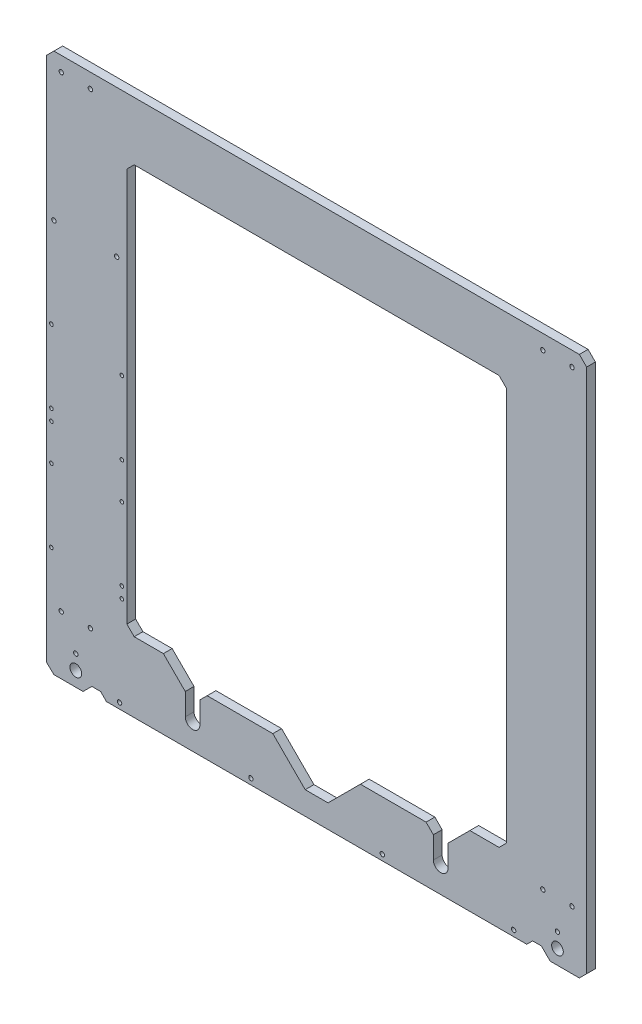
SolidWorks part; units mm, degrees
material "Lega 1060"
ref_plane "Piano frontale" through (0, 0, 0) normal (0, 0, 1) x (1, 0, 0)
ref_plane "Piano superiore" through (0, 0, 0) normal (0, 1, 0) x (1, 0, 0)
ref_plane "Piano destro" through (0, 0, 0) normal (1, 0, 0) x (0, 0, -1)
sketch "FRAME" plane through (0, 0, 0) normal (0, 0, 1) x (1, 0, 0)
  line L0 (0, 4.8083) -> (0, 365)
  line L1 (5, 370) -> (365, 370)
  line L2 (370, 365) -> (370, 5)
  line L3 (365, 0) -> (345, 0)
  line L4 (5, 0) -> (0, 4.8083)
  line L5 (0, 4.8083) -> (0, 365)
  line L6 (0, 365) -> (5, 370)
  line L7 (5, 370) -> (365, 370)
  line L8 (365, 370) -> (370, 365)
  line L9 (370, 365) -> (370, 5)
  line L10 (370, 5) -> (365, 0)
  line L11 (365, 0) -> (345, 0)
  line L12 (345, 0) -> (343, 2)
  line L13 (329, 2) -> (41, 2)
  line L14 (27, 2) -> (25, 0)
  line L15 (25, 0) -> (5, 0)
  line L16 (95, 20) -> (95, 35)
  line L17 (95, 35) -> (80, 50)
  line L18 (80, 50) -> (60, 50)
  line L19 (60, 50) -> (55, 55)
  line L20 (55, 55) -> (55, 325)
  line L21 (55, 325) -> (60, 330)
  line L22 (60, 330) -> (310, 330)
  line L23 (310, 330) -> (315, 325)
  line L24 (315, 325) -> (315, 55)
  line L25 (315, 55) -> (310, 50)
  line L26 (105, 20) -> (105, 35)
  line L27 (105, 35) -> (110, 40)
  line L28 (310, 50) -> (290, 50)
  line L29 (290, 50) -> (275, 35)
  line L30 (275, 35) -> (275, 20)
  line L31 (265, 20) -> (265, 35)
  line L32 (265, 35) -> (260, 40)
  line L33 (177.1751, 17.8249) -> (192.8249, 17.8249)
  line L34 (192.8249, 17.8249) -> (215, 40)
  line L35 (177.1751, 17.8249) -> (155, 40)
  line L36 (110, 40) -> (155, 40)
  line L37 (215, 40) -> (260, 40)
  line L105 (340, 360) -> (360, 360) construction
  line L178 (343, 2) -> (339, 6)
  line L179 (339, 6) -> (333, 6)
  line L180 (333, 6) -> (329, 2)
  line L181 (27, 2) -> (31, 6)
  line L182 (31, 6) -> (37, 6)
  line L183 (37, 6) -> (41, 2)
  line L196 (25, 0) -> (5, 0)
  line L198 (355, 0) -> (404.0551, 0) construction
  line L199 (290, 370) -> (404.0551, 370) construction
  arc A0 (95, 20) -> (105, 20) centre (100, 20) ccw
  arc A1 (265, 20) -> (275, 20) centre (270, 20) ccw
  circle A2 centre (3.2951, 74.61) radius 1.25
  circle A3 centre (51.5551, 150.81) radius 1.25
  circle A4 centre (3.2951, 157.16) radius 1.25
  circle A5 centre (3.2951, 149.54) radius 1.25
  circle A6 centre (3.2951, 124.61) radius 1.25
  circle A7 centre (51.5551, 125.88) radius 1.25
  circle A8 centre (51.5551, 200.81) radius 1.25
  circle A9 centre (3.2951, 207.16) radius 1.25
  circle A16 centre (50, 6) radius 1.5
  circle A17 centre (320, 6) radius 1.5
  circle A18 centre (230, 6) radius 1.5
  circle A19 centre (140, 6) radius 1.5
  circle A20 centre (20, 10) radius 4
  circle A21 centre (350, 10) radius 4
  circle A26 centre (10, 40) radius 1.5
  circle A27 centre (30, 40) radius 1.5
  circle A28 centre (20, 20) radius 1.5
  circle A29 centre (350, 20) radius 1.5
  circle A30 centre (340, 40) radius 1.5
  circle A31 centre (360, 40) radius 1.5
  circle A32 centre (360, 360) radius 1.5
  circle A33 centre (340, 360) radius 1.5
  circle A34 centre (10, 360) radius 1.5
  circle A35 centre (30, 360) radius 1.5
  circle A46 centre (51.5551, 75.88) radius 1.25
  circle A47 centre (51.5551, 68.26) radius 1.25
  circle A50 centre (5, 269.5) radius 1.5
  circle A51 centre (48, 269.5) radius 1.5
  point P0 (51.5551, 150.81)
  point P1 (3.2951, 149.54)
  point P2 (51.5551, 68.26)
  point P3 (3.2951, 74.61)
  point P194 (3.2951, 157.16)
  point P195 (51.5551, 75.88)
  dimension "D8" = 370
sketch "ANCORS" [suppressed] plane through (0, 0, 0) normal (0, 0, 1) x (1, 0, 0)
  line L1 (170.0247, 235) -> (170.0247, 194) construction
  line L2 (170.0247, 214.5) -> (158.9936, 214.5) construction
  circle A0 centre (120.7826, 212.556) radius 2
  circle A1 centre (216.1502, 212.556) radius 2
  circle A2 centre (167.2683, 270.0641) radius 2
  circle A3 centre (167.2683, 156.9648) radius 2
  circle A4 centre (120.7826, 90.4425) radius 2
  circle A5 centre (216.1502, 90.4425) radius 2
  circle A6 centre (170.0247, 214.5) radius 2
  dimension "D1" = 4
extrude "Boss-Extrude1" add sketch "FRAME" along normal blind 6 contours L182 L183 L13 L180 L179 L178 L12 L3 L10 L2 L8 L1 L6 L0 L4 L15 L14 L181 A51 A50 A47 A46 A35 A34 A33 A32 A31 A30 A29 A28 A27 A26 A21 A20
